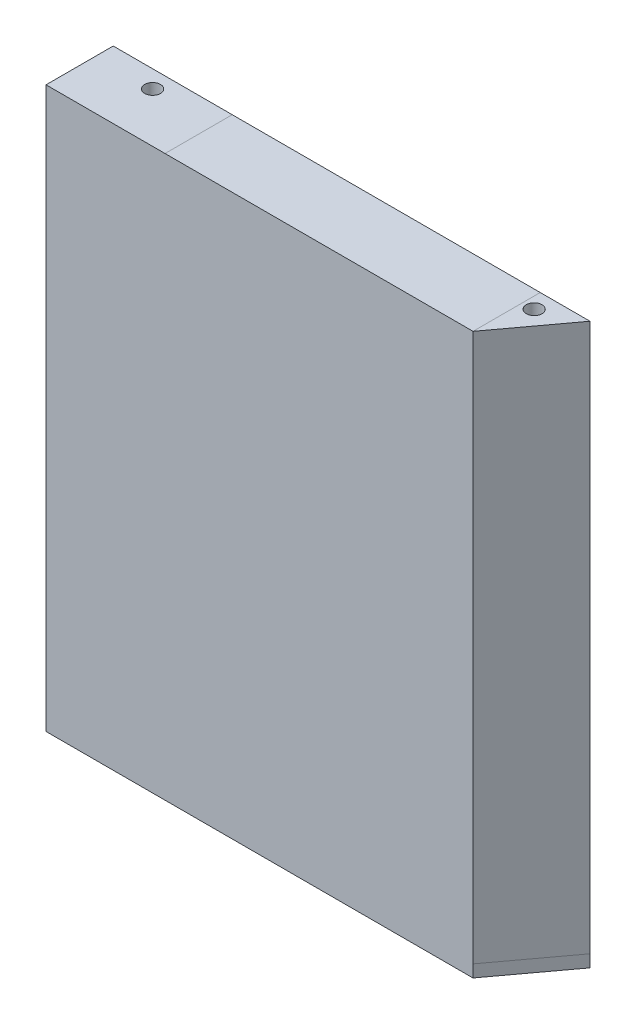
SolidWorks part; units mm, degrees
ref_plane "Płaszczyzna XY" through (0, 0, 0) normal (0, 0, 1) x (1, 0, 0)
ref_plane "Płaszczyzna XZ" through (0, 0, 0) normal (0, 1, 0) x (1, 0, 0)
ref_plane "Płaszczyzna YZ" through (0, 0, 0) normal (1, 0, 0) x (0, 0, -1)
ref_plane "Plane1" through (0, 0, 156.4) normal (0, 0, 1) x (1, 0, 0)
sketch "Sketch1" plane through (0, 0, 156.4) normal (0, 0, 1) x (1, 0, 0)
  line L0 (-125.6727, 154.6293) -> (48.3273, 154.6359) construction
  line L1 (-125.6727, 154.6293) -> (48.3273, 154.6359)
  line L2 (50.2841, 147.636) -> (50.2952, 154.636) construction
  line L3 (50.2841, 147.636) -> (50.2952, 154.636)
  line L4 (50.3068, -151.364) -> (-184.6611, -151.373) construction
  line L5 (50.2841, -151.364) -> (-184.6611, -151.373)
  line L6 (-186.6708, 104.627) -> (-186.6705, 97.627) construction
  line L7 (-186.6708, 104.627) -> (-186.6705, 97.627)
  line L8 (-125.6727, 154.6293) -> (-186.6708, 154.6293)
  line L9 (-186.6708, 154.6293) -> (-186.6708, 104.627)
  line L10 (-186.6705, 97.627) -> (-186.6705, -151.373)
  line L11 (-184.6611, -151.373) -> (-186.6705, -151.373)
  line L12 (50.2952, 154.636) -> (48.3273, 154.6359)
  line L13 (50.2841, 147.636) -> (50.2841, -151.364)
extrude "Boss-Extrude1" add sketch "Sketch1" along normal blind 7
sketch "Sketch2" plane through (0, 0, 163.4) normal (0, 0, 1) x (1, 0, 0)
  line L0 (-125.6728, 161.6293) -> (-193.6708, 161.6293)
  line L1 (-193.6708, 161.6293) -> (-193.6708, 104.6269)
  line L2 (-193.6708, 104.6269) -> (-193.6705, 97.6269)
  line L3 (-193.6705, 97.6269) -> (-193.6705, -158.373)
  line L4 (-193.6705, -158.373) -> (-184.6609, -158.373)
  line L5 (-184.6609, -158.373) -> (50.2841, -158.364)
  line L8 (50.3063, 161.636) -> (-125.6728, 161.6293)
  line L9 (-125.6727, 154.6293) -> (-186.6708, 154.6293)
  line L10 (-186.6708, 154.6293) -> (-186.6708, 104.627)
  line L11 (-186.6708, 104.627) -> (-186.6705, 97.627)
  line L12 (-186.6705, 97.627) -> (-186.6705, -151.373)
  line L13 (-186.6705, -151.373) -> (-184.6611, -151.373)
  line L14 (-184.6611, -151.373) -> (50.2841, -151.364)
  line L15 (50.2841, -151.364) -> (50.2841, 147.636)
  line L16 (50.2841, 147.636) -> (50.2952, 154.636)
  line L17 (50.2952, 154.636) -> (-125.6727, 154.6293)
  line L18 (-125.6727, 154.6293) -> (-186.6708, 154.6293)
  line L19 (-186.6708, 154.6293) -> (-186.6708, 104.627)
  line L20 (-186.6708, 104.627) -> (-186.6705, 97.627)
  line L21 (-186.6705, 97.627) -> (-186.6705, -151.373)
  line L22 (-186.6705, -151.373) -> (-184.6611, -151.373)
  line L23 (-184.6611, -151.373) -> (50.2841, -151.364)
  line L25 (50.2841, 147.636) -> (50.2952, 154.636) construction
  line L26 (50.2952, 154.636) -> (-125.6727, 154.6293)
  line L27 (50.2841, -151.364) -> (50.2841, -158.364)
  line L28 (50.2952, 154.636) -> (50.3063, 161.636)
  line L30 (57.3063, 161.6362) -> (-125.6728, 161.6293) construction
  line L31 (-184.6609, -158.373) -> (57.2841, -158.3638) construction
  line L36 (57.2841, -158.3638) -> (57.2841, 147.6304) construction
  line L37 (57.2841, 147.6304) -> (57.3063, 161.6362) construction
  line L38 (50.2841, -151.364) -> (50.2841, 147.636) construction
  dimension "D1" = 0
  dimension "D2" = 7
extrude "Boss-Extrude2" add sketch "Sketch2" against normal up to vertex (38.4 mm away)
sketch "Sketch3" plane through (-0.0062, 161.634, 0) normal (0, 1, 0) x (1, 0, 0)
  line L0 (50.3124, -125) -> (50.3124, -163.4) construction
  line L1 (50.3124, -125) -> (50.3124, -163.4)
  line L2 (50.3124, -125) -> (78.7124, -125)
  line L3 (78.7124, -125) -> (50.3124, -163.4)
  dimension "D1" = 28.4
extrude "Boss-Extrude3" add sketch "Sketch3" against normal blind 7 separate body
sketch "Sketch4" plane through (0.006, -158.366, 0) normal (0, -1, 0) x (1, 0, 0)
  line L0 (50.278, 125) -> (50.278, 163.4) construction
  line L1 (50.278, 125) -> (50.278, 163.4)
  line L2 (50.278, 125) -> (78.678, 125)
  line L3 (78.678, 125) -> (50.278, 163.4)
  dimension "D1" = 28.4
extrude "Boss-Extrude4" add sketch "Sketch4" against normal blind 7
sketch "Sketch5" plane through (-0.0059, 154.634, 0) normal (0, -1, 0) x (1, 0, 0)
  line L0 (50.3124, 163.4) -> (78.7124, 125) construction
  line L1 (50.3124, 163.4) -> (78.7124, 125)
  line L4 (50.3124, 156.4) -> (73.5354, 125)
  line L8 (73.5354, 125) -> (78.7124, 125)
  line L9 (50.3124, 156.4) -> (50.3124, 163.4)
  dimension "D1" = 7
extrude "Boss-Extrude13" add sketch "Sketch5" along normal blind 306
sketch "Sketch6" plane through (-193.6705, 0, 0) normal (-1, 0, 0) x (0, 0, 1)
  spline S0 degree 3 poles (135.76, -114.5943) (135.76, -128.8743) (150.04, -128.8743) (150.04, -114.5943) (150.04, -100.3143) (135.76, -100.3143) (135.76, -114.5943) (135.76, -128.8743) (150.04, -128.8743) knots -0.5 0 0 0 0.5 0.5 0.5 1 1 1 1.5 1.5 1.5 weights 1 0.333333 0.333333 1 0.333333 0.333333 1 0.333333 0.333333 only from (135.76, -114.5943) to (135.76, -114.5943) construction
  spline S1 degree 3 poles (135.76, -114.5943) (135.76, -128.8743) (150.04, -128.8743) (150.04, -114.5943) (150.04, -100.3143) (135.76, -100.3143) (135.76, -114.5943) (135.76, -128.8743) (150.04, -128.8743) knots -0.5 0 0 0 0.5 0.5 0.5 1 1 1 1.5 1.5 1.5 weights 1 0.333333 0.333333 1 0.333333 0.333333 1 0.333333 0.333333 only from (135.76, -114.5943) to (135.76, -114.5943)
extrude "Cut-Extrude1" cut sketch "Sketch6" against normal up to next (7 mm away)
sketch "Sketch7" plane through (0.006, -158.366, 0) normal (0, -1, 0) x (1, 0, 0)
  line L0 (-184.667, 125) -> (78.678, 125) construction
  line L1 (-193.6766, 125) -> (-193.6766, 163.4) construction
  circle A0 centre (-161.1766, 135) radius 4.5
  circle A1 centre (56.8234, 135) radius 4.5
  dimension "D1" = 9
  dimension "D4" = 9
  dimension "D2" = 10
  dimension "D3" = 32.5
  dimension "D5" = 10
  dimension "D6" = 218
extrude "Cut-Extrude2" cut sketch "Sketch7" against normal through all
